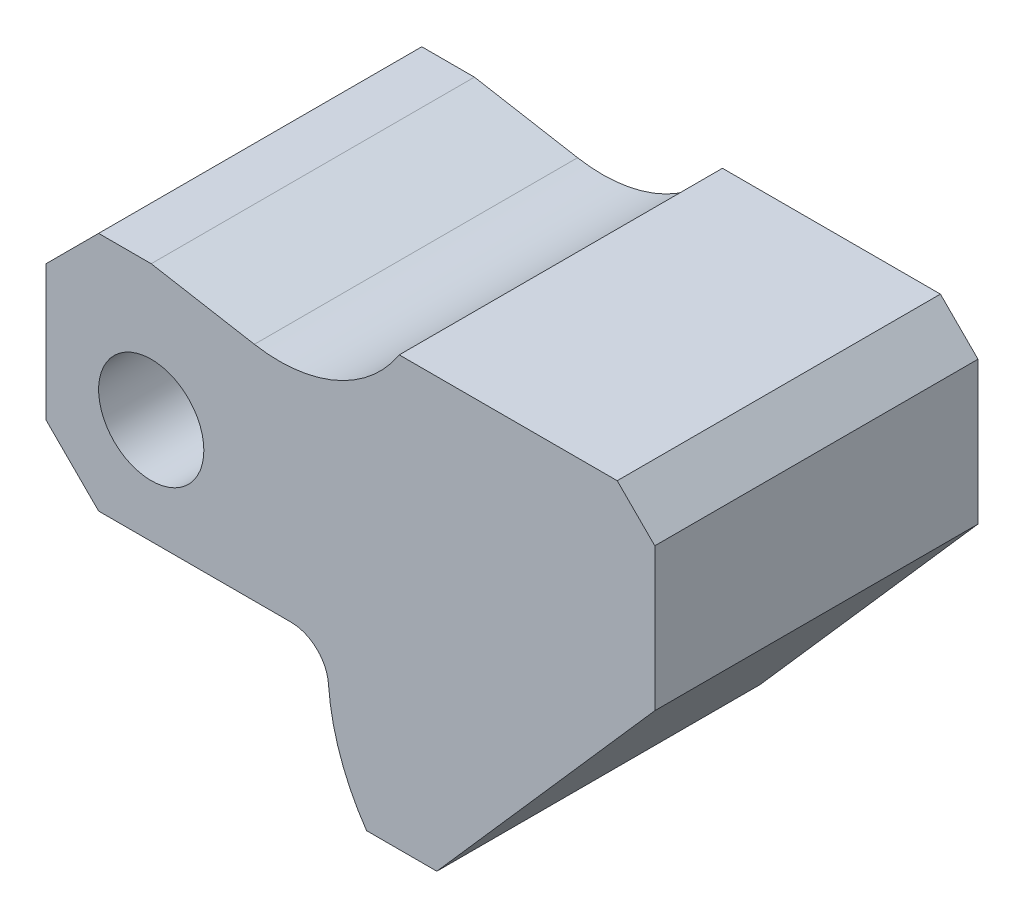
SolidWorks part; units mm, degrees
material "AISI 1020"
ref_plane "Front Plane" through (0, 0, 0) normal (0, 0, 1) x (1, 0, 0)
ref_plane "Top Plane" through (0, 0, 0) normal (0, 1, 0) x (1, 0, 0)
ref_plane "Right Plane" through (0, 0, 0) normal (1, 0, 0) x (0, 0, -1)
sketch "Sketch2" plane through (0, 0, 0) normal (0, 0, 1) x (1, 0, 0)
  line L7 (-14, 11) -> (-14, -7)
  line L8 (-14, -7) -> (-7, -14)
  line L9 (-7, -14) -> (18.592, -14)
  line L10 (-14, 11) -> (-7, 18)
  line L12 (-7, 18) -> (0, 18)
  line L13 (0, 18) -> (13.7287, 15.5793)
  line L14 (33, 24) -> (62, 24)
  line L15 (62, 24) -> (67, 19)
  line L16 (67, 19) -> (67, 0)
  line L17 (67, 0) -> (38, -33)
  line L18 (38, -33) -> (28.6515, -33)
  circle A2 centre (0, 0) radius 7
  arc A3 (13.7287, 15.5793) -> (33, 24) centre (17.028, 34.2906) ccw
  arc A4 (23.5785, -18.6324) -> (28.6515, -33) centre (52.5, -16.5) ccw
  arc A5 (18.592, -14) -> (23.5785, -18.6324) centre (18.592, -19) cw
  dimension "D11" = 10
  dimension "D13" = 14
  dimension "D17" = 29
  dimension "D1" = 14
  dimension "D10" = 19
  dimension "D12" = 5
  dimension "D9" = 45
  dimension "D2" = 7
  dimension "D3" = 7
  dimension "D4" = 45
  dimension "D5" = 45
  dimension "D6" = 14
  dimension "D7" = 14
  dimension "D8" = 32
  dimension "D14" = 29
  dimension "D15" = 57
  dimension "D16" = 5
  dimension "D18" = 29
  dimension "D19" = 81
  dimension "D20" = 24
  dimension "D21" = 19
extrude "Boss-Extrude1" add sketch "Sketch2" along normal blind 43
equation "\"A\"= 81"
equation "\"B\"= 57"
equation "\"C\"= 43"
